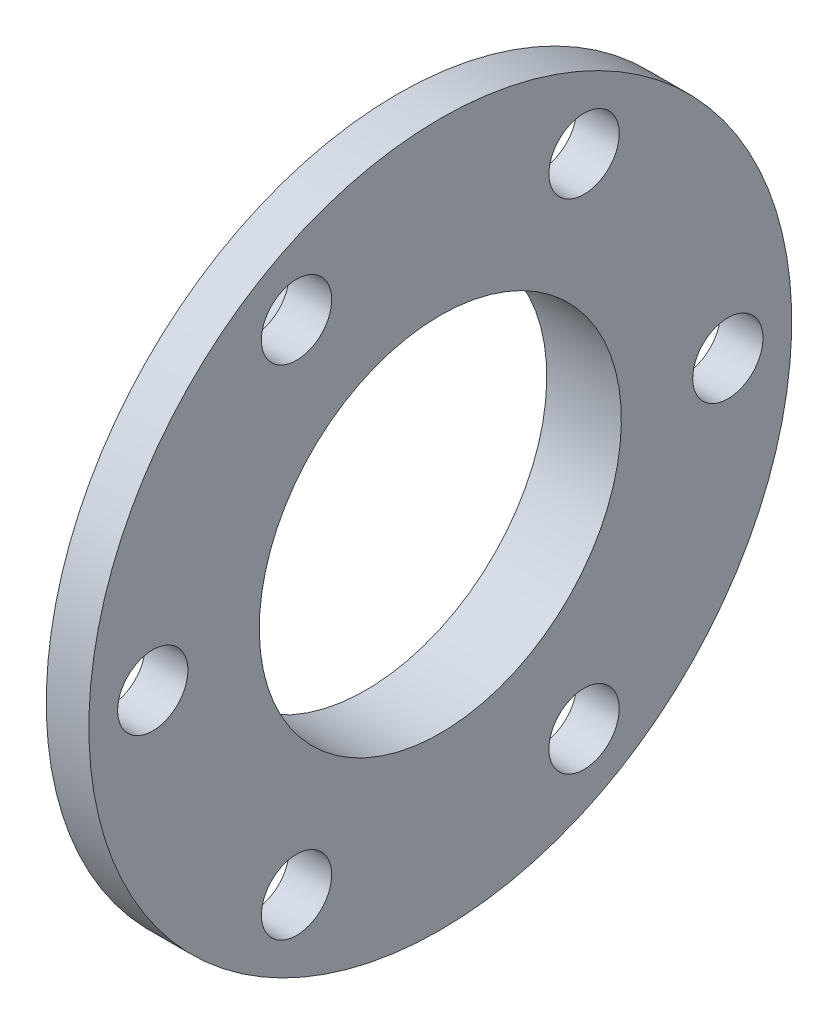
SolidWorks part; units mm, degrees
material "1.0036 (S235JRG1)"
ref_plane "Front Plane" through (0, 0, 0) normal (0, 0, 1) x (1, 0, 0)
ref_plane "Top Plane" through (0, 0, 0) normal (0, 1, 0) x (1, 0, 0)
ref_plane "Right Plane" through (0, 0, 0) normal (1, 0, 0) x (0, 0, -1)
sketch "Sketch2" plane through (0, 0, 0) normal (0, 0, 1) x (1, 0, 0)
  line L0 (0, 0) -> (-7, 0) construction
  line L1 (-7, 0) -> (-7, 21)
  line L2 (-7, 21) -> (-4, 21)
  line L3 (-4, 21) -> (-4, 33)
  line L4 (-4, 33) -> (0, 33)
  line L5 (0, 33) -> (0, 0)
  line L6 (0, 0) -> (-7, 0) construction
  line L8 (-7, 17) -> (0, 17)
  dimension "D1" = 4
  dimension "D2" = 3
  dimension "D3" = 42
  dimension "D4" = 12
  dimension "D5" = 34
revolve "Revolve1" add sketch "Sketch2" angle 360 about L0
sketch "Sketch3" plane through (-4, 0, 0) normal (-1, 0, 0) x (0, 0, 1)
  point P0 (-27, 0)
  dimension "D1" = 27
hole_wizard "M6 Clearance Hole1" positions "3DSketch1" profile "Sketch4" hole size "M6" standard "ISO" end condition up to next
sketch3d "3DSketch1"
  point P0 (-4, 0, -27)
sketch "Sketch4" plane through (-4, 0, -27) normal (0, 1, 0) x (0, 0, 1)
  line L0 (0, 0) -> (0, 4)
  line L1 (0, 4) -> (3.3, 4)
  line L2 (3.3, 4) -> (3.3, 0)
  line L5 (3.3, 0) -> (0, 0)
  line L11 (0, -6.35) -> (0, 107.95) construction
  dimension "Thru Hole Dia." = 6.6
  dimension "Thru Hole Depth" = 4
pattern_circular "CirPattern1" count 6 over 360 about axis through (0, 0, 0) along (1, 0, 0) of "M6 Clearance Hole1"
